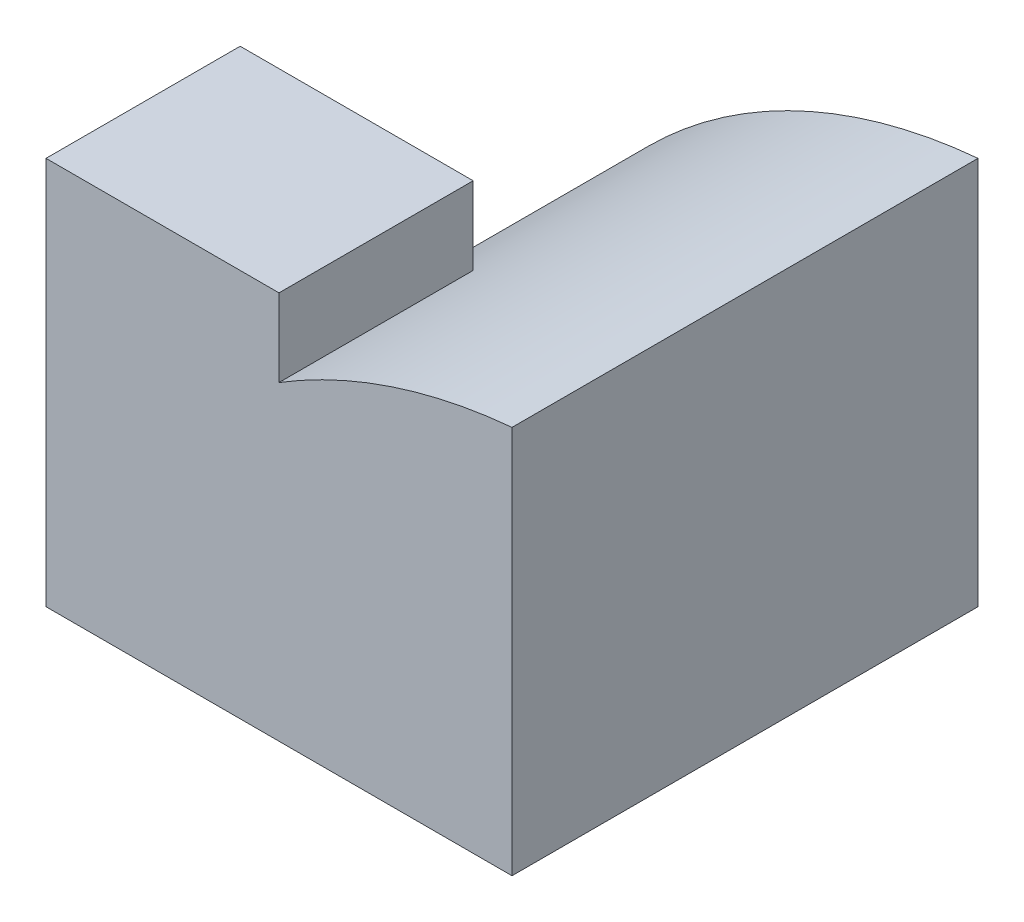
SolidWorks part; units mm, degrees
ref_plane "Front" through (0, 0, 0) normal (0, 0, 1) x (1, 0, 0)
ref_plane "Top" through (0, 0, 0) normal (0, 1, 0) x (1, 0, 0)
ref_plane "Right" through (0, 0, 0) normal (1, 0, 0) x (0, 0, -1)
sketch "Sketch1" plane through (0, 0, 0) normal (0, 1, 0) x (1, 0, 0)
  line L1 (-3, -3) -> (3, -3)
  line L2 (-3, -3) -> (-3, 3)
  line L3 (-3, 3) -> (3, 3)
  line L4 (3, -3) -> (3, 3)
  line L5 (-3, -3) -> (3, 3) construction
  line L6 (-3, 3) -> (3, -3) construction
  point P0 (0, 0)
  dimension "D1" = 6
  dimension "D2" = 6
extrude "Boss-Extrude1" add sketch "Sketch1" along normal blind 5
sketch "Sketch13" plane through (0, 0, -3) normal (0, 0, -1) x (-1, 0, 0)
  line L0 (3, 0) -> (-3, 0) construction
  line L1 (-3, 5) -> (-3, 0) construction
  line L6 (-3, 0) -> (3, 0)
  line L7 (-3, 5) -> (-3, 0)
  line L8 (3, 5) -> (-3, 5)
  line L9 (3, 0) -> (3, 5)
  line L10 (-3, 0) -> (3, 0)
  line L11 (-3, 5) -> (-3, 0)
  line L12 (3, 5) -> (-3, 5)
  line L13 (3, 0) -> (3, 5)
  arc A0 (-3, 5) -> (3, 0) centre (-3.6111, -1.8333) cw
  point P3 (0, 4)
  line M6 (3, 0) -> (3, 5)
  line M7 (3, 5) -> (-3, 5)
  dimension "D1" = 4
  dimension "D2" = 3
  dimension "D3" = 0
extrude "Cut-Extrude12" cut sketch "Sketch13" against normal blind 3.5 contours A0 M7 M6
sketch "Sketch14" plane through (0, 0, 0.5) normal (0, 0, -1) x (-1, 0, 0)
  line L0 (0, 4) -> (0, 5)
  line L2 (3, 5) -> (-3, 5)
  line L3 (3, 0) -> (3, 5)
  line L4 (3, 5) -> (-3, 5)
  line L5 (3, 0) -> (3, 5)
  arc A1 (3, 0) -> (-3, 5) centre (-3.6111, -1.8333) ccw
  arc A2 (3, 0) -> (-3, 5) centre (-3.6111, -1.8333) ccw
  line M4 (3, 5) -> (-3, 5)
  arc M5 (-3, 5) -> (3, 0) centre (-3.6111, -1.8333) cw
  dimension "D1" = 0
extrude "Cut-Extrude13" cut sketch "Sketch14" against normal blind 3.5 contours L0 M5 M4
